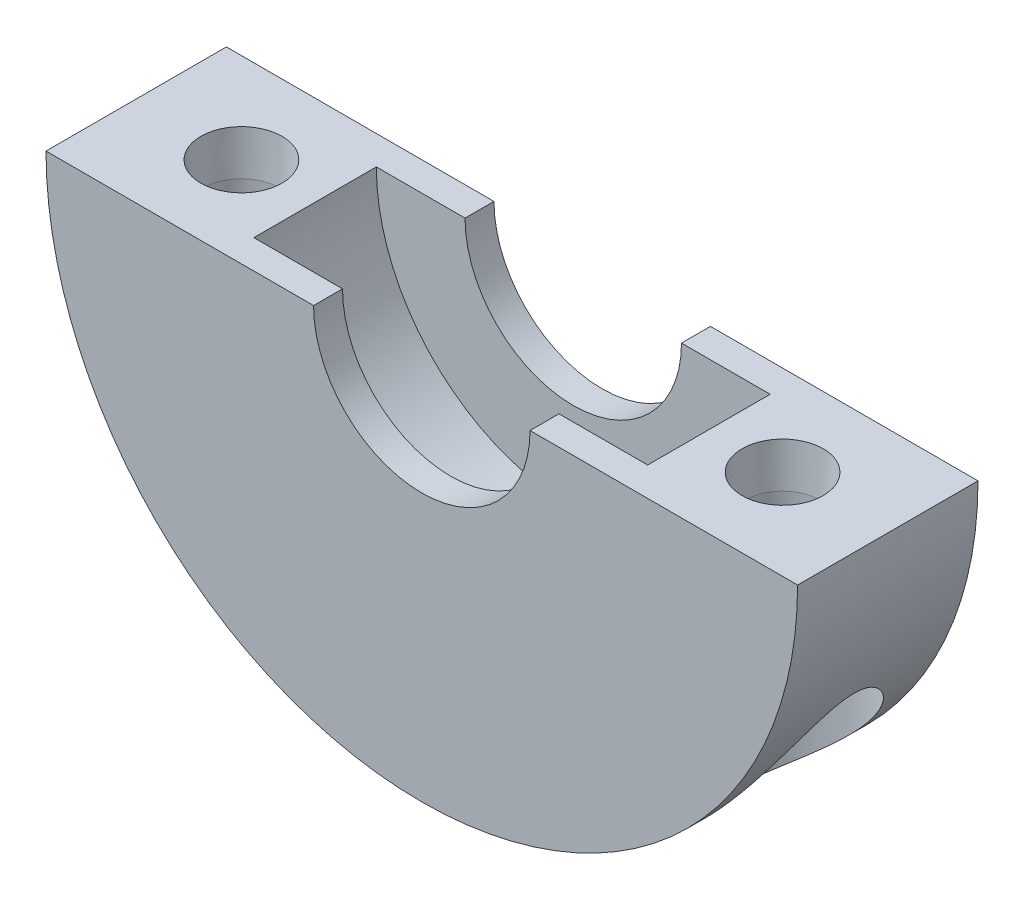
SolidWorks part; units mm, degrees
ref_plane "Front Plane" through (0, 0, 0) normal (0, 0, 1) x (1, 0, 0)
ref_plane "Top Plane" through (0, 0, 0) normal (0, 1, 0) x (1, 0, 0)
ref_plane "Right Plane" through (0, 0, 0) normal (1, 0, 0) x (0, 0, -1)
sketch "Sketch1" plane through (0, 0, 0) normal (0, 0, 1) x (1, 0, 0)
  line L0 (-25, 0) -> (-9.1, 0)
  line L1 (9.1, 0) -> (25, 0)
  line L11 (-9.1, 0) -> (9.2113, 0)
  line L12 (-25, 0) -> (25, 0)
  arc A0 (-25, 0) -> (25, 0) centre (0, 0) ccw
  dimension "D1" = 25
extrude "Boss-Extrude1" add sketch "Sketch1" along normal blind 12 contours L0 A0 L1 L11
ref_plane "Plane1" through (0, -40, 0) normal (0, 1, 0) x (1, 0, 0)
sketch "Sketch2" plane through (0, -40, 0) normal (0, 1, 0) x (1, 0, 0)
  line L1 (-25, -12) -> (25, -12) construction
  circle A0 centre (-18, -6) radius 4.75
  circle A1 centre (18, -6) radius 4.75
  dimension "D1" = 9.5
  dimension "D2" = 9.5
  dimension "D3" = 6
  dimension "D4" = 6
  dimension "D5" = 18
  dimension "D6" = 18
extrude "Cut-Extrude1" cut sketch "Sketch2" along normal blind 35 contours A1 | A0
sketch "Sketch3" plane through (0, -5, 0) normal (0, -1, 0) x (1, 0, 0)
  circle A0 centre (18, 6) radius 2.05
  circle A1 centre (-18, 6) radius 2.05
  dimension "D1" = 4.1
  dimension "D2" = 4.1
extrude "Cut-Extrude2" cut sketch "Sketch3" against normal blind 35
sketch "Sketch4" plane through (0, 0, 0) normal (0, 1, 0) x (1, 0, 0)
  line L0 (-25, -12) -> (25, -12) construction
  line L1 (0, 0) -> (-7.2, 0)
  line L2 (0, 0) -> (0, -12)
  line L3 (0, -12) -> (-7.2, -12)
  line L4 (-7.2, 0) -> (-7.2, -12)
  line L6 (-7.2, -1.925) -> (-13.1, -1.925)
  line L7 (-7.2, -1.925) -> (-7.2, -10.075)
  line L8 (-7.2, -10.075) -> (-13.1, -10.075)
  line L9 (-13.1, -1.925) -> (-13.1, -10.075)
  dimension "D1" = 8.15
  dimension "D2" = 1.925
  dimension "D3" = 7.2
  dimension "D4" = 13.1
revolve "Cut-Revolve1" cut sketch "Sketch4" angle 360 about L2
hole_wizard "CSK for M3 Cross Countersunk Head Screw1" positions "Sketch5" profile "Sketch6" countersink size "M3" standard "AS" end condition through all
sketch "Sketch5" plane through (0, 0, 0) normal (0, 1, 0) x (1, 0, 0)
  point P0 (18, -6)
  point P3 (-18, -6)
sketch "Sketch6" plane through (18, 0, 6) normal (1, 0, 0) x (0, 0, 1)
  line L0 (0, 0) -> (0, 25)
  line L1 (0, 25) -> (2.5, 25)
  line L2 (2.5, 25) -> (2.5, 2.8601)
  line L3 (2.5, 2.8601) -> (2.7, 0)
  line L5 (2.7, 0) -> (0, 0)
  line L6 (-2.5, 2.8601) -> (-2.7, 0) construction
  line L11 (0, -6.35) -> (0, 107.95) construction
  dimension "Thru Hole Dia." = 5
  dimension "Thru Hole Depth" = 25
  dimension "Near C'Sink Dia." = 5.4
  dimension "Near C'Sink Angle" = 8
